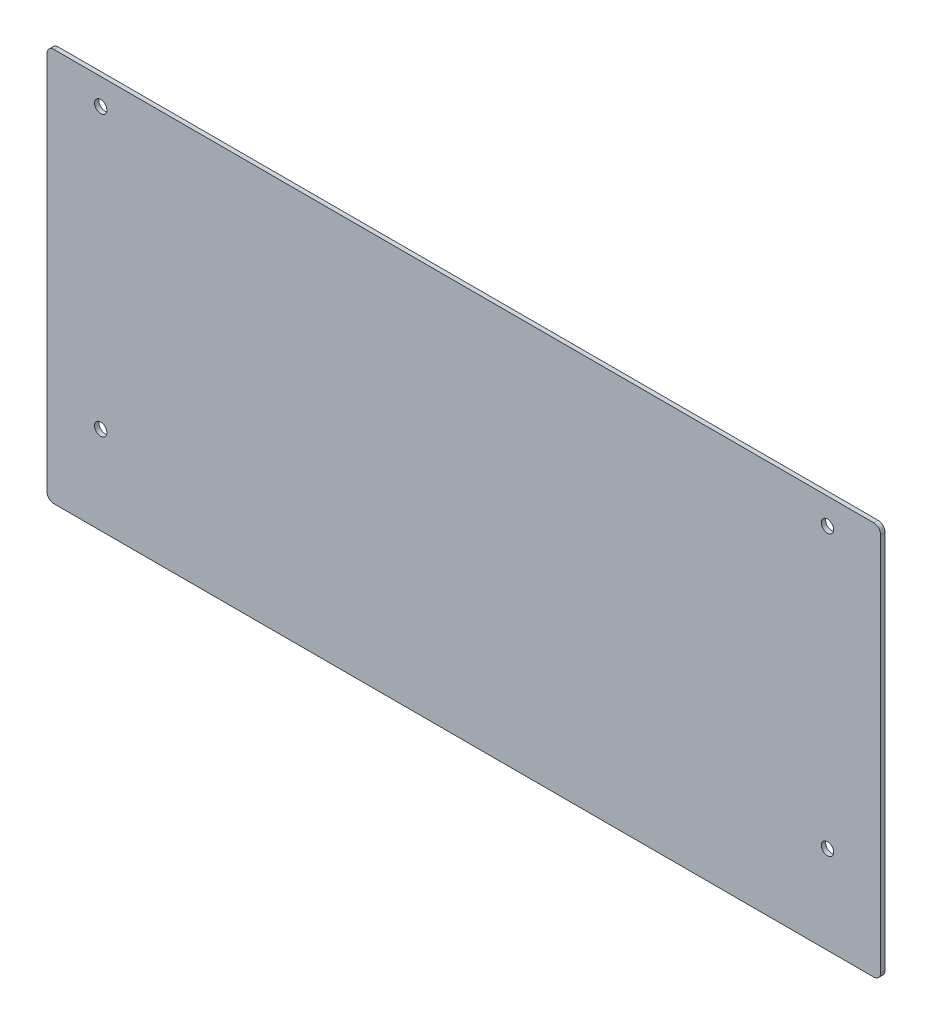
SolidWorks part; units mm, degrees
material "ABS PC"
ref_plane "X-Y Datum" through (0, 0, 0) normal (0, 0, 1) x (1, 0, 0)
ref_plane "X-Z Datum" through (0, 0, 0) normal (0, 1, 0) x (1, 0, 0)
ref_plane "Y-Z Datum" through (0, 0, 0) normal (1, 0, 0) x (0, 0, -1)
sketch "Sketch1" plane through (0, 0, 0) normal (0, 0, 1) x (1, 0, 0)
  line L1 (10.4879, -305.1211) -> (314.9661, -305.1211)
  line L2 (10.4879, -305.1211) -> (10.4879, -161.4279)
  line L3 (10.4879, -161.4279) -> (314.9661, -161.4279)
  line L4 (314.9661, -305.1211) -> (314.9661, -161.4279)
  circle A0 centre (30.1061, -170.9529) radius 1.9638
  circle A1 centre (295.5361, -170.9529) radius 1.7798
  circle A2 centre (295.5361, -272.9789) radius 1.6122
  circle A3 centre (30.1061, -272.9789) radius 1.6824
extrude "Boss-Extrude1" add sketch "Sketch1" along normal blind 1.5875
fillet "Fillet1" radius 2.54 4 edges at (10.4879, -305.1211, 0.7937) (10.4879, -161.4279, 0.7937) (314.9661, -161.4279, 0.7937) (314.9661, -305.1211, 0.7937)
hole_wizard "M4 Clearance Hole1" positions "Sketch2" profile "Sketch3" hole size "M4" standard "ANSI Metric" end condition through all
sketch "Sketch2" plane through (0, 0, 1.5875) normal (0, 0, 1) x (1, 0, 0)
  point P0 (30.1061, -170.9529)
  point P3 (30.1061, -272.9789)
  point P6 (295.5361, -170.9529)
  point P9 (295.5361, -272.9789)
sketch "Sketch3" plane through (30.1061, -170.9529, 1.5875) normal (1, 0, 0) x (0, -1, 0)
  line L0 (0, 0) -> (0, 1.5875)
  line L1 (0, 1.5875) -> (2.25, 1.5875)
  line L2 (2.25, 1.5875) -> (2.25, 0)
  line L5 (2.25, 0) -> (0, 0)
  line L11 (0, -6.35) -> (0, 107.95) construction
  dimension "Thru Hole Dia." = 4.5
  dimension "Thru Hole Depth" = 1.5875
